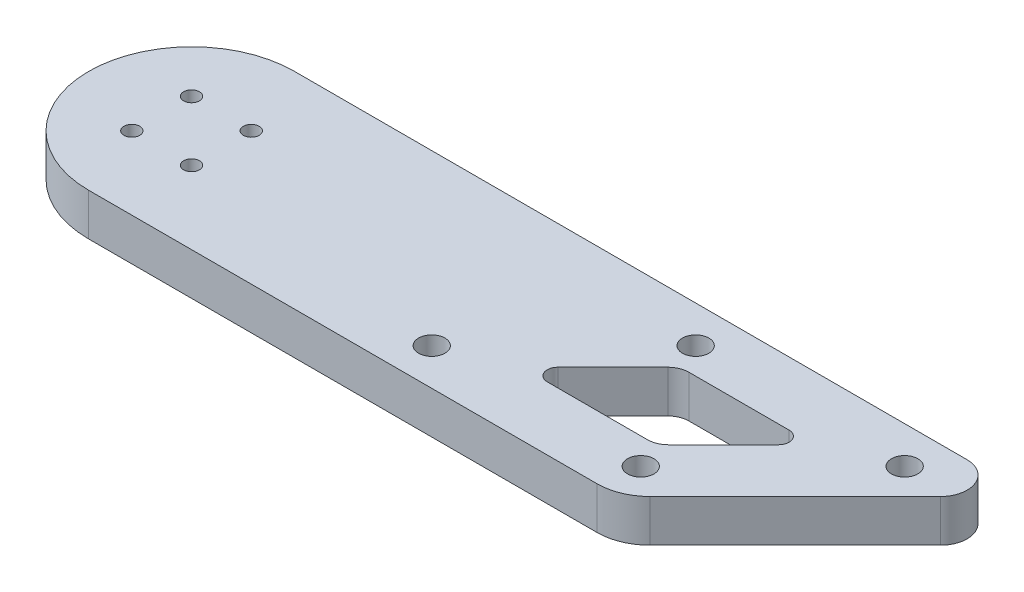
SolidWorks part; units mm, degrees
ref_plane "前视基准面" through (0, 0, 0) normal (0, 0, 1) x (1, 0, 0)
ref_plane "上视基准面" through (0, 0, 0) normal (0, 1, 0) x (1, 0, 0)
ref_plane "右视基准面" through (0, 0, 0) normal (1, 0, 0) x (0, 0, -1)
sketch "草图1" plane through (0, 0, 0) normal (0, 1, 0) x (1, 0, 0)
  line L0 (0, 0) -> (120, 0) construction
  line L1 (0, 19.5) -> (127.4289, 19.5)
  line L2 (-5.6569, 5.6569) -> (5.6569, 5.6569) construction
  line L3 (-5.6569, 5.6569) -> (-5.6569, -5.6569) construction
  line L4 (-5.6569, -5.6569) -> (5.6569, -5.6569) construction
  line L5 (5.6569, 5.6569) -> (5.6569, -5.6569) construction
  line L6 (-5.6569, 5.6569) -> (5.6569, -5.6569) construction
  line L7 (-5.6569, -5.6569) -> (5.6569, 5.6569) construction
  line L8 (0, -19.5) -> (96.3579, -19.5)
  line L9 (130.9645, 10.9645) -> (103.4289, -16.5711)
  circle A0 centre (0, 0) radius 19.5 construction
  arc A1 (0, 19.5) -> (0, -19.5) centre (0, 0) ccw
  circle A2 centre (-5.6569, 5.6569) radius 1.5
  circle A3 centre (5.6569, 5.6569) radius 1.5
  circle A4 centre (5.6569, -5.6569) radius 1.5
  circle A5 centre (-5.6569, -5.6569) radius 1.5
  arc A6 (96.3579, -19.5) -> (103.4289, -16.5711) centre (96.3579, -9.5) ccw
  arc A7 (127.4289, 19.5) -> (130.9645, 10.9645) centre (127.4289, 14.5) cw
  point P15 (0, 0)
  dimension "D1" = 39
  dimension "D3" = 3
  dimension "D5" = 10
  dimension "D6" = 5
  dimension "D2" = 16
  dimension "D4" = 135
  dimension "D7" = 120
extrude "凸台-拉伸1" add sketch "草图1" along normal blind 8
sketch "草图2" plane through (0, 8, 0) normal (0, 1, 0) x (1, 0, 0)
  line L0 (73.4878, -4.0858) -> (83.902, 6.3284)
  line L1 (86.7304, 7.5) -> (105.701, 7.5)
  line L2 (107.1152, 4.0858) -> (96.701, -6.3284)
  line L3 (93.8726, -7.5) -> (74.902, -7.5)
  arc A0 (74.902, -7.5) -> (73.4878, -4.0858) centre (74.902, -5.5) cw
  arc A1 (93.8726, -7.5) -> (96.701, -6.3284) centre (93.8726, -3.5) ccw
  arc A2 (107.1152, 4.0858) -> (105.701, 7.5) centre (105.701, 5.5) ccw
  arc A3 (86.7304, 7.5) -> (83.902, 6.3284) centre (86.7304, 3.5) ccw
extrude "切除-拉伸1" cut sketch "草图2" against normal through all both and the other way through all
sketch "草图3" plane through (0, 8, 0) normal (0, 1, 0) x (1, 0, 0)
  circle A0 centre (58.0025, -12.5) radius 2.5
  circle A1 centre (83.0025, 12.5) radius 2.5
  circle A2 centre (97.6005, -12.5) radius 2.5
  circle A3 centre (122.6005, 12.5) radius 2.5
extrude "切除-拉伸2" cut sketch "草图3" against normal through all both and the other way through all
